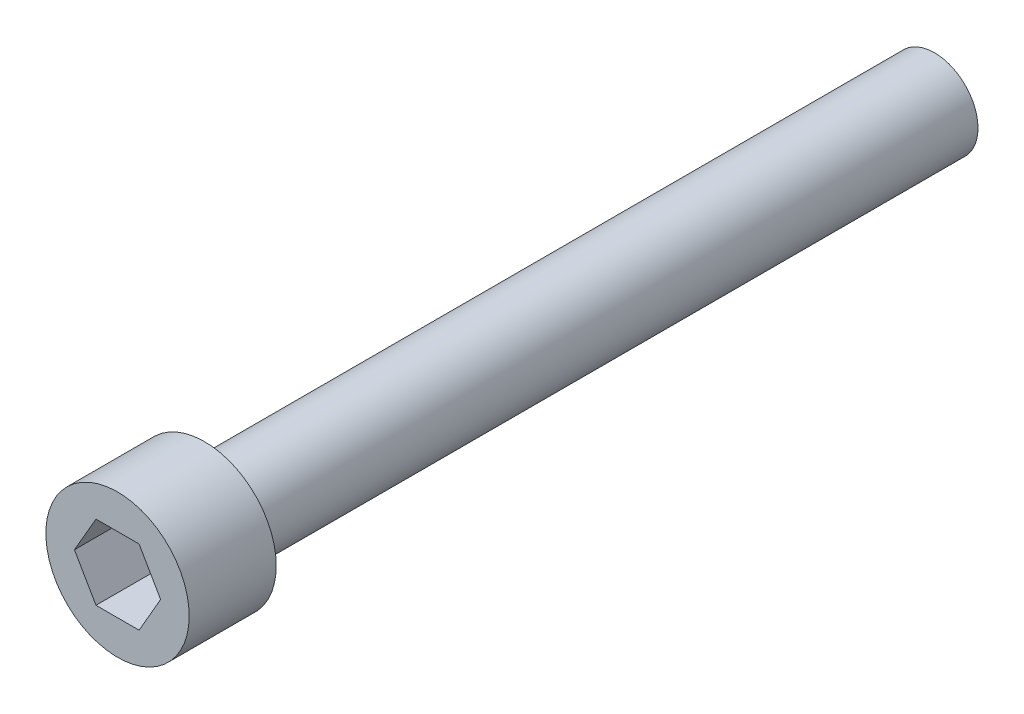
SolidWorks part; units mm, degrees
material "AISI 4340 Steel, normalized"
ref_plane "Front Plane" through (0, 0, 0) normal (0, 0, 1) x (1, 0, 0)
ref_plane "Top Plane" through (0, 0, 0) normal (0, 1, 0) x (1, 0, 0)
ref_plane "Right Plane" through (0, 0, 0) normal (1, 0, 0) x (0, 0, -1)
sketch "Sketch1" plane through (0, 0, 0) normal (0, 1, 0) x (1, 0, 0)
  line L0 (0, 0) -> (0, 39.0906)
  line L1 (0, 39.0906) -> (2.0828, 39.0906)
  line L2 (2.0828, 39.0906) -> (2.0828, 4.1656)
  line L3 (2.0828, 4.1656) -> (3.429, 4.1656)
  line L4 (3.429, 4.1656) -> (3.429, 0)
  line L5 (3.429, 0) -> (0, 0)
  dimension "D1" = 2.0828
  dimension "D2" = 3.429
  dimension "D3" = 4.1656
  dimension "D4" = 34.925
revolve "Revolve1" add sketch "Sketch1" angle 360 about L0
sketch "Sketch2" plane through (0, 0, 0) normal (0, 0, 1) x (1, 0, 0)
  line L1 (2.0622, 0) -> (1.0311, 1.7859)
  line L2 (1.0311, 1.7859) -> (-1.0311, 1.7859)
  line L3 (-1.0311, 1.7859) -> (-2.0622, 0)
  line L4 (-2.0622, 0) -> (-1.0311, -1.7859)
  line L5 (-1.0311, -1.7859) -> (1.0311, -1.7859)
  line L6 (1.0311, -1.7859) -> (2.0622, 0)
  circle A0 centre (0, 0) radius 1.7859 construction
  dimension "D1" = 3.5719
extrude "9-64 allen" cut sketch "Sketch2" against normal blind 3.175
